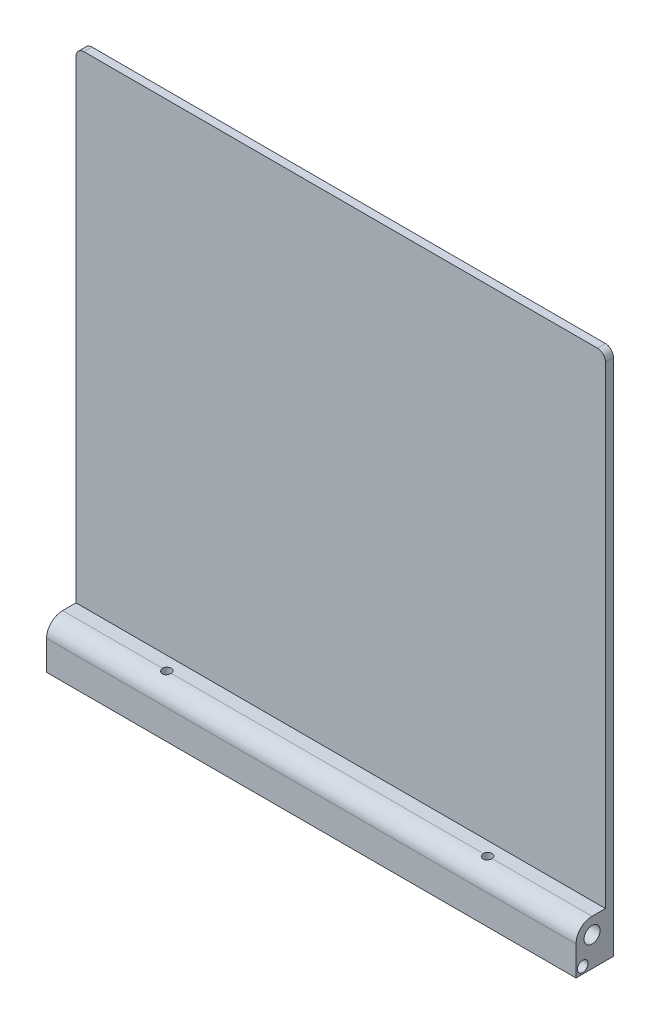
SolidWorks part; units mm, degrees
ref_plane "Front Plane" through (0, 0, 0) normal (0, 0, 1) x (1, 0, 0)
ref_plane "Top Plane" through (0, 0, 0) normal (0, 1, 0) x (1, 0, 0)
ref_plane "Right Plane" through (0, 0, 0) normal (1, 0, 0) x (0, 0, -1)
sketch "Sketch1" plane through (0, 0, 0) normal (0, 0, 1) x (1, 0, 0)
  line L1 (0, 0) -> (198, 0)
  line L2 (0, 0) -> (0, 180)
  line L3 (0, 180) -> (198, 180)
  line L4 (198, 0) -> (198, 180)
  dimension "D1" = 198
  dimension "D2" = 180
  dimension "D3" = 198
extrude "Boss-Extrude1" add sketch "Sketch1" along normal blind 3
sketch "Sketch3" plane through (0, 0, 0) normal (-1, 0, 0) x (0, 0, 1)
  line L0 (8, -3) -> (8, -6) construction
  line L2 (0, 180) -> (0, 0) construction
  line L3 (0, 0) -> (8, 0)
  line L4 (0, 0) -> (0, -12)
  line L5 (0, -12) -> (8, -12)
  line L9 (3, 0) -> (0, 0) construction
  circle A0 centre (8, -6) radius 3
  arc A1 (8, -12) -> (8, 0) centre (8, -6) ccw
  dimension "D1" = 6
  dimension "D2" = 12
  dimension "D3" = 8
extrude "Boss-Extrude2" add sketch "Sketch3" against normal up to surface (198 mm away) up to face at (198, 90, 1.5)
ref_plane "Plane1" through (99, 0, 0) normal (-1, 0, 0) x (0, 0, 1)
sketch "Sketch4" plane through (0, 0, 0) normal (0, -1, 0) x (1, 0, 0)
  line L0 (198, 0) -> (0, 0) construction
  line L1 (0, 0) -> (198, 0)
  line L2 (0, 0) -> (0, 3)
  line L3 (0, 3) -> (198, 3)
  line L4 (198, 0) -> (198, 3)
  line L5 (0, 3) -> (0, 0) construction
  line L6 (198, 3) -> (198, 0) construction
  line L7 (198, 3) -> (0, 3) construction
sketch "Sketch12" plane through (0, 0, 0) normal (0, 1, 0) x (1, 0, 0)
  circle A0 centre (39, -8) radius 1.65
  circle A1 centre (159, -8) radius 1.65
  circle A2 centre (39, -8) radius 1.25 construction
  circle A3 centre (159, -8) radius 1.25 construction
  dimension "D1" = 3.3
extrude "Cut-Extrude1" cut sketch "Sketch12" against normal blind 5
extrude "Boss-Extrude3" add sketch "Sketch4" along normal blind 17
sketch "Sketch10" plane through (0, 0, 3) normal (0, 0, 1) x (1, 0, 0)
  line L0 (0, -17) -> (0, -12) construction
  line L1 (0, -17) -> (198, -17)
  line L2 (0, -17) -> (0, -15)
  line L3 (0, -15) -> (198, -15)
  line L4 (198, -17) -> (198, -15)
  line L5 (198, 0) -> (198, 180) construction
  line L6 (198, -17) -> (0, -17) construction
  dimension "D1" = 2
extrude "Boss-Extrude7" add sketch "Sketch10" along normal blind 10
sketch "Sketch11" plane through (0, 0, 0) normal (-1, 0, 0) x (0, 0, 1)
  line L0 (11, -6) -> (14, -6)
  line L9 (0, -17) -> (14, -17)
  line L10 (0, -17) -> (0, -6)
  line L11 (0, -6) -> (5, -6)
  line L12 (14, -17) -> (14, -6)
  circle A0 centre (8, -6) radius 3 construction
  arc A1 (5, -6) -> (11, -6) centre (8, -6) ccw
  arc A5 (8, -12) -> (8, 0) centre (8, -6) ccw construction
fillet "Fillet2" radius 3 4 edges at (198, 180, 1.5) (0, 180, 1.5) (0, -17, 6.5) (198, -17, 6.5)
extrude "Boss-Extrude8" add sketch "Sketch11" against normal up to surface (198 mm away) up to face at (198, 37.75, 4.25)
sketch "Sketch15" plane through (198, 0, 0) normal (1, 0, 0) x (0, 0, -1)
  line L0 (-14, -6) -> (-14, -17) construction
  line L1 (-14, -17) -> (0, -17) construction
  circle A0 centre (-8, -6) radius 6.5 construction
  circle A1 centre (-11.5, -14.5) radius 2
  dimension "D1" = 13
  dimension "D2" = 4
  dimension "D3" = 2.5
  dimension "D4" = 2.5
extrude "Cut-Extrude4" cut sketch "Sketch15" against normal blind 4
mirror "Mirror3" about plane through (99, 0, 0) normal (-1, 0, 0) of "Cut-Extrude4"
